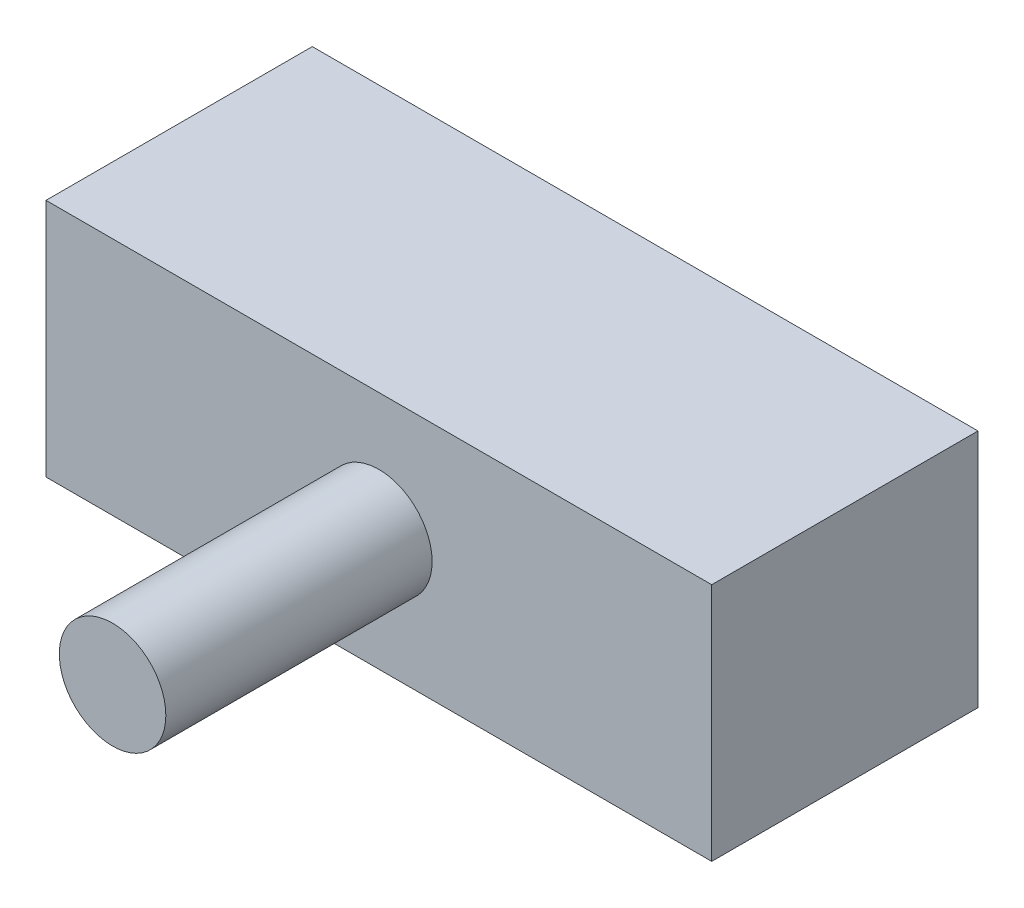
SolidWorks part; units mm, degrees
ref_plane "Front Plane" through (0, 0, 0) normal (0, 0, 1) x (1, 0, 0)
ref_plane "Top Plane" through (0, 0, 0) normal (0, 1, 0) x (1, 0, 0)
ref_plane "Right Plane" through (0, 0, 0) normal (1, 0, 0) x (0, 0, -1)
sketch "Sketch1" plane through (0, 0, 0) normal (0, 0, 1) x (1, 0, 0)
  line L1 (-12.5, 4.5) -> (12.5, 4.5)
  line L2 (-12.5, 4.5) -> (-12.5, -4.5)
  line L3 (-12.5, -4.5) -> (12.5, -4.5)
  line L4 (12.5, 4.5) -> (12.5, -4.5)
  line L5 (-12.5, 4.5) -> (12.5, -4.5) construction
  line L6 (-12.5, -4.5) -> (12.5, 4.5) construction
  point P0 (0, 0)
  dimension "D1" = 9
  dimension "D2" = 25
extrude "Boss-Extrude1" add sketch "Sketch1" along normal blind 10
ref_plane "Plane1" through (0, 0, 10) normal (0, 0, 1) x (1, 0, 0)
sketch "Sketch2" plane through (0, 0, 10) normal (0, 0, 1) x (1, 0, 0)
  circle A0 centre (0, 0) radius 2
  dimension "D1" = 4
extrude "Boss-Extrude2" add sketch "Sketch2" along normal blind 10 contours A0
